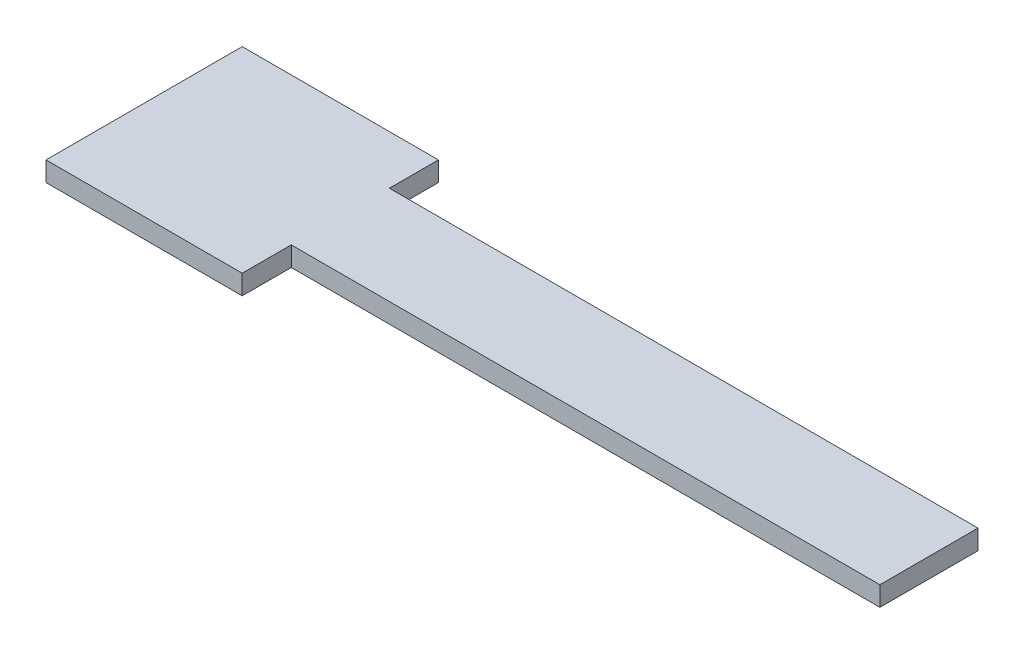
SolidWorks part; units mm, degrees
ref_plane "Front Plane" through (0, 0, 0) normal (0, 0, 1) x (1, 0, 0)
ref_plane "Top Plane" through (0, 0, 0) normal (0, 1, 0) x (1, 0, 0)
ref_plane "Right Plane" through (0, 0, 0) normal (1, 0, 0) x (0, 0, -1)
sketch "Sketch1" plane through (0, 0, 0) normal (0, 1, 0) x (1, 0, 0)
  line L1 (0, 0) -> (60, 0)
  line L2 (0, 0) -> (0, 10)
  line L3 (0, 10) -> (60, 10)
  line L4 (60, 0) -> (60, 10)
extrude "Extrude1" add sketch "Sketch1" along normal blind 2
sketch "Sketch2" plane through (0, 2, 0) normal (0, 1, 0) x (-1, 0, 0)
  line L1 (0, -15) -> (20, -15)
  line L2 (0, -15) -> (0, 5)
  line L3 (0, 5) -> (20, 5)
  line L4 (20, -15) -> (20, 5)
  line L5 (-60, -10) -> (0, -10) construction
  dimension "D1" = 20
  dimension "D2" = 5
extrude "Extrude2" add sketch "Sketch2" against normal blind 2
